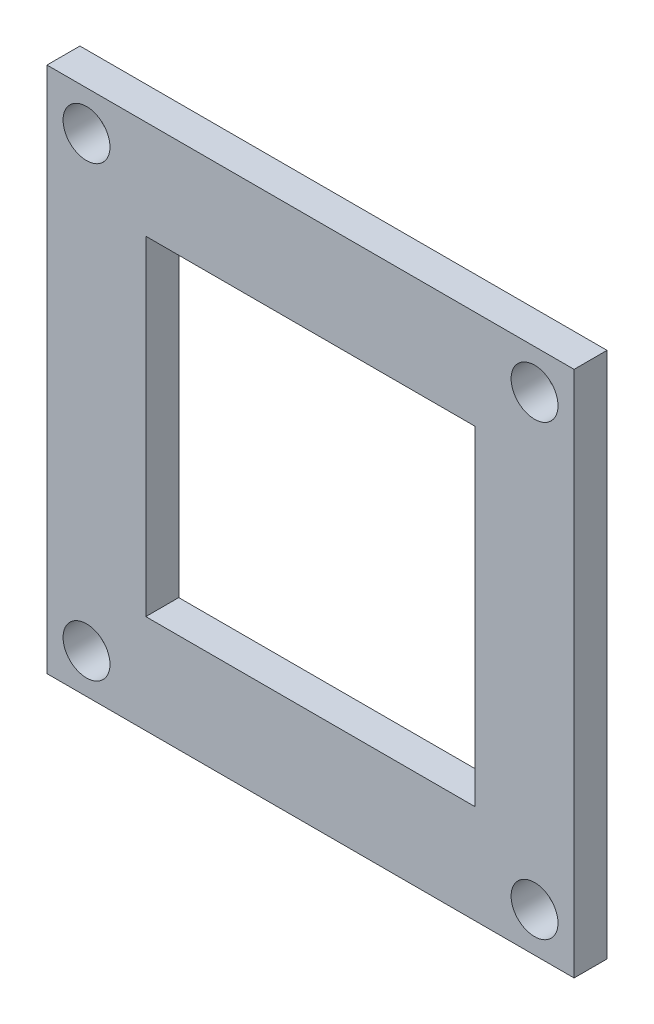
SolidWorks part; units mm, degrees
material "6061-T6 (SS)"
ref_plane "Front Plane" through (0, 0, 0) normal (0, 0, 1) x (1, 0, 0)
ref_plane "Top Plane" through (0, 0, 0) normal (0, 1, 0) x (1, 0, 0)
ref_plane "Right Plane" through (0, 0, 0) normal (1, 0, 0) x (0, 0, -1)
sketch "Sketch1" plane through (0, 0, 0) normal (0, 0, 1) x (1, 0, 0)
  line L1 (-7.9375, 7.9375) -> (7.9375, 7.9375)
  line L2 (-7.9375, 7.9375) -> (-7.9375, -7.9375)
  line L3 (-7.9375, -7.9375) -> (7.9375, -7.9375)
  line L4 (7.9375, 7.9375) -> (7.9375, -7.9375)
  line L5 (-7.9375, 7.9375) -> (7.9375, -7.9375) construction
  line L6 (-7.9375, -7.9375) -> (7.9375, 7.9375) construction
  line L7 (-12.7, 12.7) -> (12.7, 12.7)
  line L8 (-12.7, 12.7) -> (-12.7, -12.7)
  line L9 (-12.7, -12.7) -> (12.7, -12.7)
  line L10 (12.7, 12.7) -> (12.7, -12.7)
  line L11 (-12.7, 12.7) -> (12.7, -12.7) construction
  line L12 (-12.7, -12.7) -> (12.7, 12.7) construction
  point P0 (0, 0)
  point P6 (0, 0)
  dimension "D1" = 15.875
  dimension "D2" = 15.875
  dimension "D3" = 25.4
  dimension "D4" = 25.4
extrude "Boss-Extrude1" add sketch "Sketch1" along normal blind 1.5875
hole_wizard "#2 Clearance Hole1" positions "Sketch2" profile "Sketch3" hole size "#2" standard "ANSI Inch" end condition through all
sketch "Sketch2" plane through (-3.3549, -31.0776, 1.5875) normal (0, 0, 1) x (1, 0, 0)
  point P0 (14.1499, 41.8726)
  point P2 (-7.4401, 41.8726)
  point P4 (-7.4401, 20.2826)
  point P6 (14.1499, 20.2826)
  point P11 (0, 0)
  point P14 (0, 0)
  point P17 (0, 0)
sketch "Sketch3" plane through (10.795, 10.795, 1.5875) normal (1, 0, 0) x (0, -1, 0)
  line L0 (0, 0) -> (0, 1.5875)
  line L1 (0, 1.5875) -> (1.1303, 1.5875)
  line L2 (1.1303, 1.5875) -> (1.1303, 0)
  line L3 (1.1303, 0) -> (0, 0)
  line L4 (0, -6.35) -> (0, 107.95) construction
  dimension "Thru Hole Dia." = 2.2606
  dimension "Thru Hole Depth" = 1.5875
